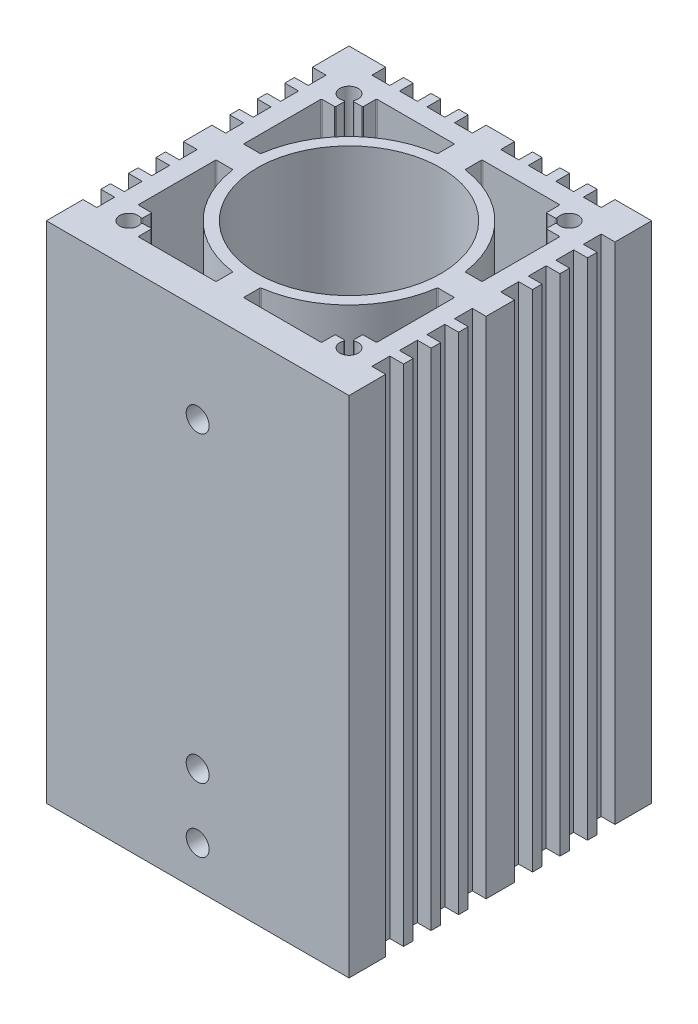
SolidWorks part; units mm, degrees
ref_plane "Alzado" through (0, 0, 0) normal (0, 0, 1) x (1, 0, 0)
ref_plane "Planta" through (0, 0, 0) normal (0, 1, 0) x (1, 0, 0)
ref_plane "Vista lateral" through (0, 0, 0) normal (1, 0, 0) x (0, 0, -1)
sketch "Croquis1" plane through (0, 0, 0) normal (0, 1, 0) x (1, 0, 0)
  line L0 (16.5, -1.55) -> (16.5, 1.55)
  line L1 (16.5, 1.55) -> (15, 1.55)
  line L2 (15, 1.55) -> (15, 3.5)
  line L3 (15, 3.5) -> (16.5, 3.5)
  line L4 (16.5, 3.5) -> (16.5, 4.55)
  line L5 (16.5, 4.55) -> (15, 4.55)
  line L6 (15, 4.55) -> (15, 6.5)
  line L7 (15, 6.5) -> (16.5, 6.5)
  line L8 (16.5, 6.5) -> (16.5, 7.55)
  line L9 (16.5, 7.55) -> (15, 7.55)
  line L10 (15, 7.55) -> (15, 9.5)
  line L11 (15, 9.5) -> (16.5, 9.5)
  line L12 (16.5, 9.5) -> (16.5, 10.55)
  line L13 (16.5, 10.55) -> (15, 10.55)
  line L14 (15, 10.55) -> (15, 12.5)
  line L15 (15, 12.5) -> (16.5, 12.5)
  line L16 (16.5, 12.5) -> (16.5, 16.5)
  line L17 (16.5, 16.5) -> (12.5, 16.5)
  line L18 (12.5, 16.5) -> (12.5, 15)
  line L19 (12.5, 15) -> (10.55, 15)
  line L20 (10.55, 15) -> (10.55, 16.5)
  line L21 (10.55, 16.5) -> (9.5, 16.5)
  line L22 (9.5, 16.5) -> (9.5, 15)
  line L23 (9.5, 15) -> (7.55, 15)
  line L24 (7.55, 15) -> (7.55, 16.5)
  line L25 (7.55, 16.5) -> (6.5, 16.5)
  line L26 (6.5, 16.5) -> (6.5, 15)
  line L27 (6.5, 15) -> (4.55, 15)
  line L28 (4.55, 15) -> (4.55, 16.5)
  line L29 (4.55, 16.5) -> (3.5, 16.5)
  line L30 (3.5, 16.5) -> (3.5, 15)
  line L31 (3.5, 15) -> (1.55, 15)
  line L32 (1.55, 15) -> (1.55, 16.5)
  line L33 (1.55, 16.5) -> (-1.55, 16.5)
  line L34 (-1.55, 16.5) -> (-1.55, 15)
  line L35 (-1.55, 15) -> (-3.5, 15)
  line L36 (-3.5, 15) -> (-3.5, 16.5)
  line L37 (-3.5, 16.5) -> (-4.55, 16.5)
  line L38 (-4.55, 16.5) -> (-4.55, 15)
  line L39 (-4.55, 15) -> (-6.5, 15)
  line L40 (-6.5, 15) -> (-6.5, 16.5)
  line L41 (-6.5, 16.5) -> (-7.55, 16.5)
  line L42 (-7.55, 16.5) -> (-7.55, 15)
  line L43 (-7.55, 15) -> (-9.5, 15)
  line L44 (-9.5, 15) -> (-9.5, 16.5)
  line L45 (-9.5, 16.5) -> (-10.55, 16.5)
  line L46 (-10.55, 16.5) -> (-10.55, 15)
  line L47 (-10.55, 15) -> (-12.5, 15)
  line L48 (-12.5, 15) -> (-12.5, 16.5)
  line L49 (-12.5, 16.5) -> (-16.5, 16.5)
  line L50 (-16.5, 16.5) -> (-16.5, 12.5)
  line L51 (-16.5, 12.5) -> (-15, 12.5)
  line L52 (-15, 12.5) -> (-15, 10.55)
  line L53 (-15, 10.55) -> (-16.5, 10.55)
  line L54 (-16.5, 10.55) -> (-16.5, 9.5)
  line L55 (-16.5, 9.5) -> (-15, 9.5)
  line L56 (-15, 9.5) -> (-15, 7.55)
  line L57 (-15, 7.55) -> (-16.5, 7.55)
  line L58 (-16.5, 7.55) -> (-16.5, 6.5)
  line L59 (-16.5, 6.5) -> (-15, 6.5)
  line L60 (-15, 6.5) -> (-15, 4.55)
  line L61 (-15, 4.55) -> (-16.5, 4.55)
  line L62 (-16.5, 4.55) -> (-16.5, 3.5)
  line L63 (-16.5, 3.5) -> (-15, 3.5)
  line L64 (-15, 3.5) -> (-15, 1.55)
  line L65 (-15, 1.55) -> (-16.5, 1.55)
  line L66 (-16.5, 1.55) -> (-16.5, -1.55)
  line L67 (-16.5, -1.55) -> (-15, -1.55)
  line L68 (-15, -1.55) -> (-15, -3.5)
  line L69 (-15, -3.5) -> (-16.5, -3.5)
  line L70 (-16.5, -3.5) -> (-16.5, -4.55)
  line L71 (-16.5, -4.55) -> (-15, -4.55)
  line L72 (-15, -4.55) -> (-15, -6.5)
  line L73 (-15, -6.5) -> (-16.5, -6.5)
  line L74 (-16.5, -6.5) -> (-16.5, -7.55)
  line L75 (-16.5, -7.55) -> (-15, -7.55)
  line L76 (-15, -7.55) -> (-15, -9.5)
  line L77 (-15, -9.5) -> (-16.5, -9.5)
  line L78 (-16.5, -9.5) -> (-16.5, -10.55)
  line L79 (-16.5, -10.55) -> (-15, -10.55)
  line L80 (-15, -10.55) -> (-15, -12.5)
  line L81 (-15, -12.5) -> (-16.5, -12.5)
  line L82 (-16.5, -12.5) -> (-16.5, -16.5)
  line L83 (-16.5, -16.5) -> (16.5, -16.5)
  line L84 (16.5, -16.5) -> (16.5, -12.5)
  line L85 (16.5, -12.5) -> (15, -12.5)
  line L86 (15, -12.5) -> (15, -10.55)
  line L87 (15, -10.55) -> (16.5, -10.55)
  line L88 (16.5, -10.55) -> (16.5, -9.5)
  line L89 (16.5, -9.5) -> (15, -9.5)
  line L90 (15, -9.5) -> (15, -7.55)
  line L91 (15, -7.55) -> (16.5, -7.55)
  line L92 (16.5, -7.55) -> (16.5, -6.5)
  line L93 (16.5, -6.5) -> (15, -6.5)
  line L94 (15, -6.5) -> (15, -4.55)
  line L95 (15, -4.55) -> (16.5, -4.55)
  line L96 (16.5, -4.55) -> (16.5, -3.5)
  line L97 (16.5, -3.5) -> (15, -3.5)
  line L98 (15, -3.5) -> (15, -1.55)
  line L99 (15, -1.55) -> (16.5, -1.55)
  line L100 (13, -9.9) -> (13, -1.6)
  line L101 (-16.5, 16.5) -> (16.5, 16.5) construction
  line L102 (-16.5, 16.5) -> (-16.5, -16.5) construction
  line L103 (-16.5, -16.5) -> (16.5, -16.5)
  line L104 (16.5, 16.5) -> (16.5, -16.5) construction
  line L105 (-16.5, 16.5) -> (16.5, -16.5) construction
  line L106 (-16.5, -16.5) -> (16.5, 16.5) construction
  line L107 (-15, -15) -> (15, -15) construction
  line L108 (-15, -15) -> (-15, 15) construction
  line L109 (-15, 15) -> (15, 15) construction
  line L110 (15, -15) -> (15, 15) construction
  line L111 (-15, -15) -> (15, 15) construction
  line L112 (-15, 15) -> (15, -15) construction
  line L113 (11.6, -10) -> (12.9, -10)
  line L114 (11.5, -10.9753) -> (11.5, -10.1)
  line L115 (10.1, -11.5) -> (10.9753, -11.5)
  line L116 (10, -12.9) -> (10, -11.6)
  line L117 (1.6, -13) -> (9.9, -13)
  line L118 (1.5, -11.2367) -> (1.5, -12.9)
  line L119 (12.9, -1.5) -> (11.2367, -1.5)
  line L120 (-9.9, -13) -> (-1.6, -13)
  line L121 (-10, -11.6) -> (-10, -12.9)
  line L122 (-10.9753, -11.5) -> (-10.1, -11.5)
  line L123 (-11.5, -10.1) -> (-11.5, -10.9753)
  line L124 (-12.9, -10) -> (-11.6, -10)
  line L125 (-13, -1.6) -> (-13, -9.9)
  line L126 (-11.2367, -1.5) -> (-12.9, -1.5)
  line L127 (-1.5, -12.9) -> (-1.5, -11.2367)
  line L128 (-13, 9.9) -> (-13, 1.6)
  line L129 (-11.6, 10) -> (-12.9, 10)
  line L130 (-11.5, 10.9753) -> (-11.5, 10.1)
  line L131 (-10.1, 11.5) -> (-10.9753, 11.5)
  line L132 (-10, 12.9) -> (-10, 11.6)
  line L133 (-1.6, 13) -> (-9.9, 13)
  line L134 (-1.5, 11.2367) -> (-1.5, 12.9)
  line L135 (-12.9, 1.5) -> (-11.2367, 1.5)
  line L136 (9.9, 13) -> (1.6, 13)
  line L137 (10, 11.6) -> (10, 12.9)
  line L138 (10.9753, 11.5) -> (10.1, 11.5)
  line L139 (11.5, 10.1) -> (11.5, 10.9753)
  line L140 (12.9, 10) -> (11.6, 10)
  line L141 (13, 1.6) -> (13, 9.9)
  line L142 (11.2367, 1.5) -> (12.9, 1.5)
  line L143 (1.5, 12.9) -> (1.5, 11.2367)
  circle A0 centre (0, 0) radius 10
  arc A1 (12.9, -10) -> (13, -9.9) centre (12.9, -9.9) ccw
  arc A2 (11.6, -10) -> (11.5, -10.1) centre (11.6, -10.1) ccw
  arc A3 (11.5, -10.9753) -> (11.6364, -11.0685) centre (11.6, -10.9753) ccw
  arc A4 (11.0685, -11.6364) -> (11.6364, -11.0685) centre (12, -12) ccw
  arc A5 (11.0685, -11.6364) -> (10.9753, -11.5) centre (10.9753, -11.6) ccw
  arc A6 (10.1, -11.5) -> (10, -11.6) centre (10.1, -11.6) ccw
  arc A7 (9.9, -13) -> (10, -12.9) centre (9.9, -12.9) ccw
  arc A8 (1.5, -12.9) -> (1.6, -13) centre (1.6, -12.9) ccw
  arc A9 (1.5859, -11.1377) -> (1.5, -11.2367) centre (1.6, -11.2367) ccw
  arc A10 (1.5859, -11.1377) -> (11.1377, -1.5859) centre (0, 0) ccw
  arc A11 (11.2367, -1.5) -> (11.1377, -1.5859) centre (11.2367, -1.6) ccw
  arc A12 (13, -1.6) -> (12.9, -1.5) centre (12.9, -1.6) ccw
  arc A13 (-10, -12.9) -> (-9.9, -13) centre (-9.9, -12.9) ccw
  arc A14 (-10, -11.6) -> (-10.1, -11.5) centre (-10.1, -11.6) ccw
  arc A15 (-10.9753, -11.5) -> (-11.0685, -11.6364) centre (-10.9753, -11.6) ccw
  arc A16 (-11.6364, -11.0685) -> (-11.0685, -11.6364) centre (-12, -12) ccw
  arc A17 (-11.6364, -11.0685) -> (-11.5, -10.9753) centre (-11.6, -10.9753) ccw
  arc A18 (-11.5, -10.1) -> (-11.6, -10) centre (-11.6, -10.1) ccw
  arc A19 (-13, -9.9) -> (-12.9, -10) centre (-12.9, -9.9) ccw
  arc A20 (-12.9, -1.5) -> (-13, -1.6) centre (-12.9, -1.6) ccw
  arc A21 (-11.1377, -1.5859) -> (-11.2367, -1.5) centre (-11.2367, -1.6) ccw
  arc A22 (-11.1377, -1.5859) -> (-1.5859, -11.1377) centre (0, 0) ccw
  arc A23 (-1.5, -11.2367) -> (-1.5859, -11.1377) centre (-1.6, -11.2367) ccw
  arc A24 (-1.6, -13) -> (-1.5, -12.9) centre (-1.6, -12.9) ccw
  arc A25 (-12.9, 10) -> (-13, 9.9) centre (-12.9, 9.9) ccw
  arc A26 (-11.6, 10) -> (-11.5, 10.1) centre (-11.6, 10.1) ccw
  arc A27 (-11.5, 10.9753) -> (-11.6364, 11.0685) centre (-11.6, 10.9753) ccw
  arc A28 (-11.0685, 11.6364) -> (-11.6364, 11.0685) centre (-12, 12) ccw
  arc A29 (-11.0685, 11.6364) -> (-10.9753, 11.5) centre (-10.9753, 11.6) ccw
  arc A30 (-10.1, 11.5) -> (-10, 11.6) centre (-10.1, 11.6) ccw
  arc A31 (-9.9, 13) -> (-10, 12.9) centre (-9.9, 12.9) ccw
  arc A32 (-1.5, 12.9) -> (-1.6, 13) centre (-1.6, 12.9) ccw
  arc A33 (-1.5859, 11.1377) -> (-1.5, 11.2367) centre (-1.6, 11.2367) ccw
  arc A34 (-1.5859, 11.1377) -> (-11.1377, 1.5859) centre (0, 0) ccw
  arc A35 (-11.2367, 1.5) -> (-11.1377, 1.5859) centre (-11.2367, 1.6) ccw
  arc A36 (-13, 1.6) -> (-12.9, 1.5) centre (-12.9, 1.6) ccw
  arc A37 (10, 12.9) -> (9.9, 13) centre (9.9, 12.9) ccw
  arc A38 (10, 11.6) -> (10.1, 11.5) centre (10.1, 11.6) ccw
  arc A39 (10.9753, 11.5) -> (11.0685, 11.6364) centre (10.9753, 11.6) ccw
  arc A40 (11.6364, 11.0685) -> (11.0685, 11.6364) centre (12, 12) ccw
  arc A41 (11.6364, 11.0685) -> (11.5, 10.9753) centre (11.6, 10.9753) ccw
  arc A42 (11.5, 10.1) -> (11.6, 10) centre (11.6, 10.1) ccw
  arc A43 (13, 9.9) -> (12.9, 10) centre (12.9, 9.9) ccw
  arc A44 (12.9, 1.5) -> (13, 1.6) centre (12.9, 1.6) ccw
  arc A45 (11.1377, 1.5859) -> (11.2367, 1.5) centre (11.2367, 1.6) ccw
  arc A46 (11.1377, 1.5859) -> (1.5859, 11.1377) centre (0, 0) ccw
  arc A47 (1.5, 11.2367) -> (1.5859, 11.1377) centre (1.6, 11.2367) ccw
  arc A48 (1.6, 13) -> (1.5, 12.9) centre (1.6, 12.9) ccw
  point P100 (0, 0)
  point P101 (0, 0)
  point P105 (0, 0)
  point P241 (-11.6364, 11.6364)
  point P242 (-11.6364, 11.6364)
  dimension "D6" = 20
  dimension "D7" = 0.1
  dimension "D8" = 1
  dimension "D9" = 11.25
  dimension "D1" = 1.55
  dimension "D2" = 3.5
  dimension "D3" = 4.55
  dimension "D4" = 15
  dimension "D5" = 16.5
  dimension "D10" = 1.5
  dimension "D11" = 10.9753
  dimension "D12" = 11.0685
extrude "Saliente-Extruir1" add sketch "Croquis1" along normal mid plane 55 contours L98 L99 L0 L1 L2 L3 L4 L5 L6 L7 L8 L9 L10 L11 L12 L13 L14 L15 L16 L17 L18 L19 L20 L21 L22 L23 L24 L25 L26 L27 L28 L29 L30 L31 L32 L33 L34 L35 L36 L37 L38 L39 L40 L41 L42 L43 L44 L45 L46 L47 L48 | L128 A36 L135 A35 A34 A33 L134 A32 L133 A31 L132 A30 L131 A29 A28 A27 L130 A26 L129 A25
sketch "Croquis2" plane through (0, 0, 16.5) normal (0, 0, 1) x (1, 0, 0)
  line L1 (-16.5, -27.5) -> (16.5, -27.5) construction
  point P2 (0, 0)
  point P10 (0, -16)
  point P11 (0, 17)
  point P12 (0, -23)
  dimension "D1" = 4.5
  dimension "D2" = 7
  dimension "D3" = 33
hole_wizard "Perforador para roscar para macho de roscar para M31" positions "Croquis3" profile "Croquis4" hole size "M3" standard "DIN"
sketch "Croquis3" plane through (0, 0, 16.5) normal (0, 0, 1) x (1, 0, 0)
  point P0 (0, 17)
  point P3 (0, -16)
  point P6 (0, -23)
sketch "Croquis4" plane through (0, 17, 16.5) normal (1, 0, 0) x (0, -1, 0)
  line L0 (0, 0) -> (0, 6.5)
  line L1 (0, 6.5) -> (1.25, 6.5)
  line L2 (1.25, 6.5) -> (1.25, 0)
  line L5 (1.25, 0) -> (0, 0)
  line L11 (0, -6.35) -> (0, 107.95) construction
  dimension "Diámetro de taladro hasta el siguiente" = 2.5
  dimension "Profundidad de taladro hasta el siguiente" = 6.5
